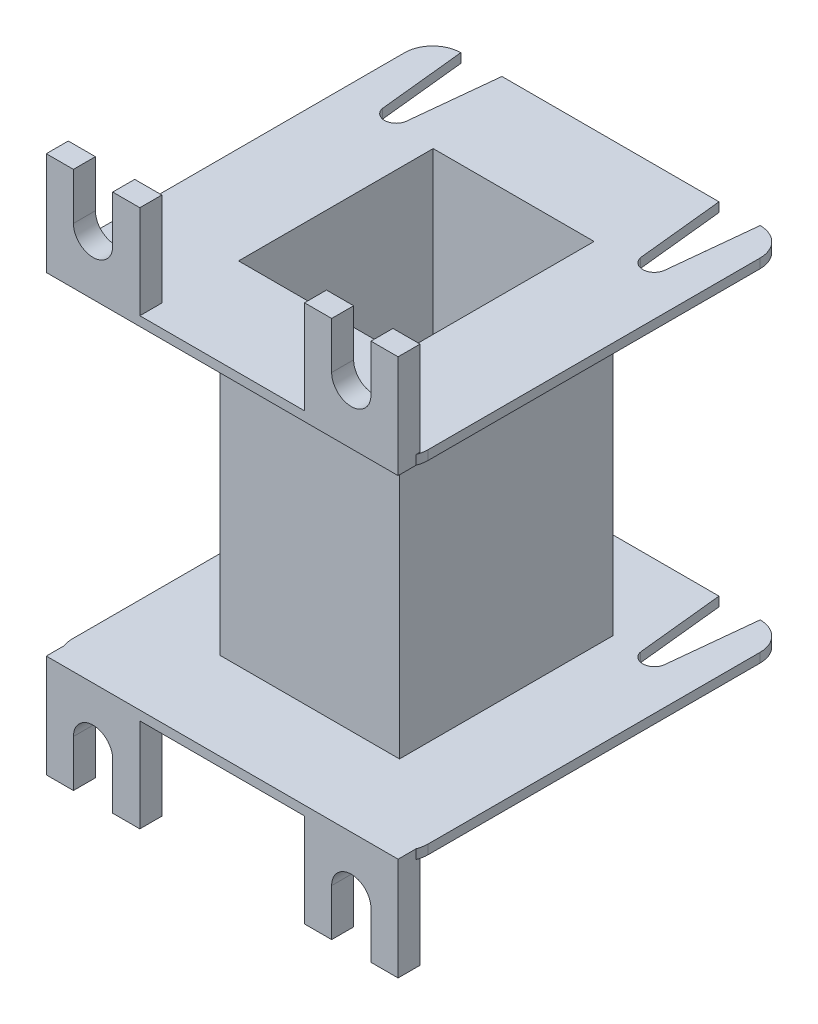
SolidWorks part; units mm, degrees
ref_plane "Front Plane" through (0, 0, 0) normal (0, 0, 1) x (1, 0, 0)
ref_plane "Top Plane" through (0, 0, 0) normal (0, 1, 0) x (1, 0, 0)
ref_plane "Right Plane" through (0, 0, 0) normal (1, 0, 0) x (0, 0, -1)
sketch "Sketch1" plane through (0, 0, 0) normal (0, 1, 0) x (1, 0, 0)
  line L1 (-8.6, -10.4) -> (8.6, -10.4)
  line L2 (-8.6, -10.4) -> (-8.6, 10.4)
  line L3 (-8.6, 10.4) -> (8.6, 10.4)
  line L4 (8.6, -10.4) -> (8.6, 10.4)
  line L5 (-8.6, -10.4) -> (8.6, 10.4) construction
  line L6 (-8.6, 10.4) -> (8.6, -10.4) construction
  line L7 (-16, -20.75) -> (16, -20.75)
  line L8 (-19, -17.75) -> (-19, 17.75)
  line L9 (-16, 20.75) -> (16, 20.75)
  line L10 (19, -17.75) -> (19, 17.75)
  line L11 (-19, -20.75) -> (19, 20.75) construction
  line L12 (-19, 20.75) -> (19, -20.75) construction
  arc A0 (-19, 17.75) -> (-16, 20.75) centre (-16, 17.75) cw
  arc A1 (19, 17.75) -> (16, 20.75) centre (16, 17.75) ccw
  arc A2 (19, -17.75) -> (16, -20.75) centre (16, -17.75) cw
  arc A3 (-16, -20.75) -> (-19, -17.75) centre (-16, -17.75) cw
  point P0 (0, 0)
  point P6 (0, 0)
  dimension "D1" = 3
extrude "Boss-Extrude1" add sketch "Sketch1" along normal blind 1
sketch "Sketch2" plane through (0, 1, 0) normal (0, 1, 0) x (1, 0, 0)
  line L0 (-8.6, -10.4) -> (-8.6, 10.4)
  line L1 (-8.6, 10.4) -> (8.6, 10.4)
  line L2 (8.6, 10.4) -> (8.6, -10.4)
  line L3 (8.6, -10.4) -> (-8.6, -10.4)
  line L4 (-9.6, -11.4) -> (-9.6, 11.4)
  line L5 (-9.6, 11.4) -> (9.6, 11.4)
  line L6 (9.6, 11.4) -> (9.6, -11.4)
  line L7 (9.6, -11.4) -> (-9.6, -11.4)
  dimension "D1" = 1
extrude "Boss-Extrude2" add sketch "Sketch2" along normal blind 35.5
sketch "Sketch3" plane through (0, 36.5, 0) normal (0, 1, 0) x (1, 0, 0)
  line L1 (-8.6, -10.4) -> (8.6, -10.4)
  line L2 (-8.6, -10.4) -> (-8.6, 10.4)
  line L3 (-8.6, 10.4) -> (8.6, 10.4)
  line L4 (8.6, -10.4) -> (8.6, 10.4)
  line L5 (-16, -20.75) -> (16, -20.75)
  line L6 (-19, -17.75) -> (-19, 17.75)
  line L7 (-16, 20.75) -> (16, 20.75)
  line L8 (19, -17.75) -> (19, 17.75)
  line L9 (-19, -20.75) -> (19, 20.75) construction
  line L10 (-19, 20.75) -> (19, -20.75) construction
  arc A0 (-19, 17.75) -> (-16, 20.75) centre (-16, 17.75) cw
  arc A1 (16, 20.75) -> (19, 17.75) centre (16, 17.75) cw
  arc A2 (19, -17.75) -> (16, -20.75) centre (16, -17.75) cw
  arc A3 (-16, -20.75) -> (-19, -17.75) centre (-16, -17.75) cw
  point P6 (0, 0)
  dimension "D1" = 3
extrude "Boss-Extrude3" add sketch "Sketch3" along normal blind 1
sketch "Sketch4" plane through (0, 37.5, 0) normal (0, 1, 0) x (-1, 0, 0)
  line L0 (8.6, 10.4) -> (19, 10.4) construction
  line L1 (19, -17.75) -> (19, 17.75) construction
  line L2 (-8.6, 10.4) -> (-19, 10.4) construction
  line L3 (-19, 17.75) -> (-19, -17.75) construction
  line L4 (8.6, -10.4) -> (19, -10.4) construction
  line L5 (-8.6, -10.4) -> (-19, -10.4) construction
  line L6 (13.8, -10.4) -> (13.8, -20.75) construction
  line L7 (-16, -20.75) -> (16, -20.75) construction
  line L8 (-13.8, -10.4) -> (-13.8, -20.75) construction
  line L9 (13.8, 10.4) -> (13.8, 20.75) construction
  line L10 (16, 20.75) -> (-16, 20.75) construction
  line L11 (-13.8, 10.4) -> (-13.8, 20.75) construction
  line L12 (16, 20.75) -> (13.8, 20.75) construction
  line L13 (13.8, 20.75) -> (11.6, 20.75) construction
  line L14 (13.8, 10.4) -> (13.8, 11.65) construction
  line L17 (19, 0) -> (-19, 0) construction
  line L18 (0, 20.75) -> (0, -20.75) construction
  line L19 (11.6, -20.75) -> (12.5726, -11.4134)
  line L20 (16, -20.75) -> (15.0274, -11.4134)
  line L23 (-11.6, -20.75) -> (-12.5726, -11.4134)
  line L24 (-16, -20.75) -> (-15.0274, -11.4134)
  line L27 (16, -20.75) -> (11.6, -20.75)
  line L28 (-11.6, -20.75) -> (-16, -20.75)
  arc A1 (12.5726, -11.4134) -> (15.0274, -11.4134) centre (13.8, -11.65) cw
  arc A3 (-12.5726, -11.4134) -> (-15.0274, -11.4134) centre (-13.8, -11.65) ccw
extrude "Cut-Extrude1" cut sketch "Sketch4" against normal through all
sketch "Sketch6" plane through (0, 36.5, 0) normal (0, -1, 0) x (1, 0, 0)
  line L0 (-8.6, 10.4) -> (-19, 10.4) construction
  line L1 (-19, -17.75) -> (-19, 17.75) construction
  line L2 (8.6, 10.4) -> (19, 10.4) construction
  line L3 (19, 17.75) -> (19, -17.75) construction
  line L4 (-13.8, 10.4) -> (-13.8, 20.75) construction
  line L5 (-16, 20.75) -> (16, 20.75) construction
  line L6 (13.8, 10.4) -> (13.8, 20.75) construction
  line L7 (-13.8, 20.75) -> (-18.8, 20.75)
  line L8 (-18.8, 20.75) -> (-18.8, 18.4)
  line L9 (-18.8, 18.4) -> (-8.8, 18.4)
  line L10 (-8.8, 18.4) -> (-8.8, 20.75)
  line L11 (-8.8, 20.75) -> (-13.8, 20.75)
  line L12 (0, 20.75) -> (0, -20.75) construction
  line L13 (11.6, -20.75) -> (-11.6, -20.75) construction
  line L14 (8.8, 18.4) -> (8.8, 20.75)
  line L15 (8.8, 20.75) -> (13.8, 20.75)
  line L16 (13.8, 20.75) -> (18.8, 20.75)
  line L17 (18.8, 20.75) -> (18.8, 18.4)
  line L18 (18.8, 18.4) -> (8.8, 18.4)
extrude "Boss-Extrude4" add sketch "Sketch6" against normal blind 11
sketch "Sketch8" plane through (0, 1, 0) normal (0, 1, 0) x (1, 0, 0)
  line L0 (-18.8, -20.75) -> (-8.8, -20.75)
  line L1 (-18.8, -20.75) -> (18.8, -20.75) construction
  line L2 (-18.8, -20.75) -> (-18.8, -18.827) construction
  line L3 (-16, -20.75) -> (16, -20.75) construction
  line L4 (-8.8, -20.75) -> (-8.8, -18.4)
  line L5 (-8.8, -18.4) -> (-18.8, -18.4)
  line L6 (-18.8, -18.4) -> (-18.8, -20.75)
  line L7 (0, 20.75) -> (0, -20.75) construction
  line L8 (11.6, 20.75) -> (-11.6, 20.75) construction
  line L9 (8.8, -20.75) -> (8.8, -18.4)
  line L10 (8.8, -18.4) -> (18.8, -18.4)
  line L11 (18.8, -20.75) -> (8.8, -20.75)
  line L12 (18.8, -18.4) -> (18.8, -20.75)
extrude "Boss-Extrude5" add sketch "Sketch8" against normal blind 11
sketch "Sketch9" plane through (0, 0, 20.75) normal (0, 0, 1) x (1, 0, 0)
  line L0 (-13.8, 47.5) -> (-13.8, -10) construction
  line L1 (-8.8, 47.5) -> (-18.8, 47.5) construction
  line L2 (-18.8, -10) -> (-8.8, -10) construction
  line L3 (13.8, 47.5) -> (13.8, -10) construction
  line L4 (18.8, 47.5) -> (8.8, 47.5) construction
  line L5 (8.8, -10) -> (18.8, -10) construction
  line L6 (-13.8, -10) -> (-13.8, -4.996) construction
  line L7 (13.8, -10) -> (13.8, -4.996) construction
  line L8 (-13.8, 47.5) -> (-13.8, 42.496) construction
  line L9 (13.8, 47.5) -> (13.8, 42.496) construction
  line L10 (0, -10) -> (0, 47.5) construction
  line L11 (0, 18.75) -> (27.3352, 18.75) construction
  line L12 (-15.9, -4.996) -> (-15.9, -10)
  line L13 (-11.7, -4.996) -> (-11.7, -10)
  line L14 (-15.9, -10) -> (-11.7, -10)
  line L15 (15.9, -10) -> (11.7, -10)
  line L16 (11.7, -4.996) -> (11.7, -10)
  line L17 (15.9, -4.996) -> (15.9, -10)
  line L18 (15.9, 47.5) -> (11.7, 47.5)
  line L19 (15.9, 42.496) -> (15.9, 47.5)
  line L20 (11.7, 42.496) -> (11.7, 47.5)
  line L21 (-15.9, 47.5) -> (-11.7, 47.5)
  line L22 (-11.7, 42.496) -> (-11.7, 47.5)
  line L23 (-15.9, 42.496) -> (-15.9, 47.5)
  arc A0 (-11.7, -4.996) -> (-15.9, -4.996) centre (-13.8, -4.996) ccw
  arc A1 (11.7, -4.996) -> (15.9, -4.996) centre (13.8, -4.996) cw
  arc A2 (11.7, 42.496) -> (15.9, 42.496) centre (13.8, 42.496) ccw
  arc A3 (-11.7, 42.496) -> (-15.9, 42.496) centre (-13.8, 42.496) cw
extrude "Cut-Extrude2" cut sketch "Sketch9" against normal through all
